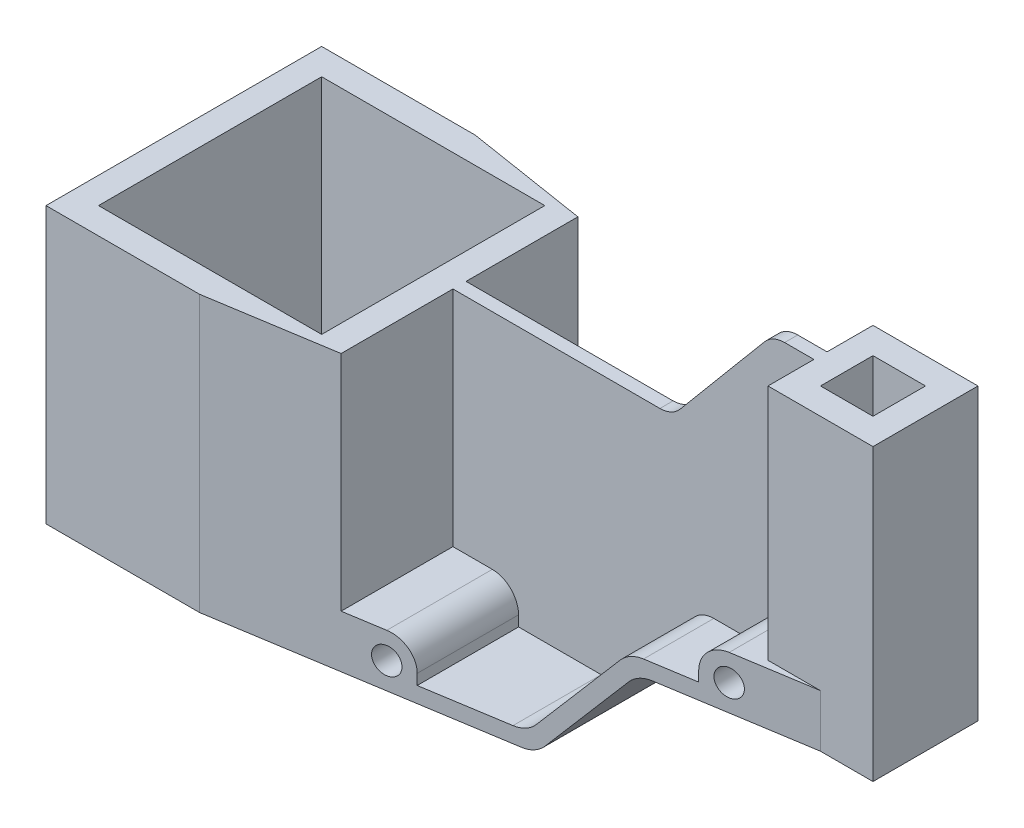
SolidWorks part; units mm, degrees
material "1060 Alloy"
ref_plane "Front Plane" through (0, 0, 0) normal (0, 0, 1) x (1, 0, 0)
ref_plane "Top Plane" through (0, 0, 0) normal (0, 1, 0) x (1, 0, 0)
ref_plane "Right Plane" through (0, 0, 0) normal (1, 0, 0) x (0, 0, -1)
sketch "Sketch1" plane through (0, 0, 0) normal (0, 0, 1) x (1, 0, 0)
  line L1 (-47.8306, 122.7704) -> (234.6694, 122.7704)
  line L2 (-47.8306, 122.7704) -> (-47.8306, -27.7296)
  line L3 (-47.8306, -27.7296) -> (234.6694, -27.7296)
  line L4 (234.6694, 122.7704) -> (234.6694, -27.7296)
extrude "Boss-Extrude2" add sketch "Sketch1" along normal blind 105
sketch "Sketch16" plane through (0, 0, 105) normal (0, 0, 1) x (1, 0, 0)
  line L5 (234.6694, -27.7296) -> (154.6694, -27.7296)
  line L6 (234.6694, -27.7296) -> (234.6694, 12.2704)
  line L7 (234.6694, 12.2704) -> (154.6694, 12.2704)
  line L8 (154.6694, -27.7296) -> (154.6694, 12.2704)
  line L13 (82.1694, 77.2704) -> (-47.8306, 77.2704)
  line L14 (82.1694, 77.2704) -> (82.1694, 122.7704)
  line L15 (82.1694, 122.7704) -> (-47.8306, 122.7704)
  line L16 (-47.8306, 77.2704) -> (-47.8306, 122.7704)
extrude "Cut-Extrude10" cut sketch "Sketch16" against normal blind 105
sketch "Sketch17" plane through (0, 122.7704, 0) normal (0, 1, 0) x (1, 0, 0)
  line L0 (234.6694, -105) -> (234.6694, 0) construction
  line L10 (214.6694, -32.5) -> (234.6694, -32.5)
  line L11 (214.6694, -32.5) -> (214.6694, 0)
  line L12 (214.6694, 0) -> (234.6694, 0)
  line L13 (234.6694, -32.5) -> (234.6694, 0)
  line L14 (214.6694, -72.5) -> (234.6694, -72.5)
  line L15 (214.6694, -72.5) -> (214.6694, -105)
  line L16 (214.6694, -105) -> (234.6694, -105)
  line L17 (234.6694, -72.5) -> (234.6694, -105)
extrude "Cut-Extrude11" cut sketch "Sketch17" against normal blind 110.5
sketch "Sketch18" plane through (0, 122.7704, 0) normal (0, 1, 0) x (1, 0, 0)
  line L0 (214.6694, -32.5) -> (194.6694, -32.5)
  line L1 (194.6694, -32.5) -> (194.6694, -50)
  line L2 (194.6694, -50) -> (82.1694, -50)
  line L3 (82.1694, 0) -> (82.1694, -105) construction
  line L4 (82.1694, -50) -> (82.1694, 0)
  line L5 (82.1694, 0) -> (214.6694, 0)
  line L6 (214.6694, 0) -> (214.6694, -32.5)
  line L7 (214.6694, -72.5) -> (194.6694, -72.5)
  line L8 (194.6694, -72.5) -> (194.6694, -55)
  line L9 (194.6694, -55) -> (82.1694, -55)
  line L10 (82.1694, -55) -> (82.1694, -105)
  line L11 (82.1694, -105) -> (214.6694, -105)
  line L12 (214.6694, -105) -> (214.6694, -72.5)
extrude "Cut-Extrude12" cut sketch "Sketch18" against normal blind 90.5
sketch "Sketch19" plane through (0, 32.2704, 0) normal (0, 1, 0) x (1, 0, 0)
  line L6 (194.6694, -55) -> (82.1694, -55) construction
  line L7 (174.6694, -55) -> (82.1694, -55)
  line L8 (82.1694, -55) -> (82.1694, -105)
  line L9 (82.1694, -105) -> (174.6694, -105)
  line L10 (82.1694, -105) -> (214.6694, -105) construction
  line L11 (174.6694, -105) -> (174.6694, -55)
extrude "Cut-Extrude13" cut sketch "Sketch19" against normal blind 14
sketch "Sketch20" plane through (0, 32.2704, 0) normal (0, 1, 0) x (1, 0, 0)
  line L0 (174.6694, -50) -> (174.6694, 0)
  line L1 (82.1694, -50) -> (194.6694, -50) construction
  line L2 (214.6694, 0) -> (82.1694, 0) construction
  line L3 (174.6694, 0) -> (82.1694, 0)
  line L4 (82.1694, 0) -> (82.1694, -50)
  line L5 (82.1694, -50) -> (174.6694, -50)
extrude "Cut-Extrude14" cut sketch "Sketch20" against normal blind 14
sketch "Sketch21" plane through (0, 77.2704, 0) normal (0, 1, 0) x (1, 0, 0)
  line L0 (-47.8306, 0) -> (82.1694, 0) construction
  line L1 (82.1694, -50) -> (57.1694, -50)
  line L2 (82.1694, -50) -> (82.1694, 0)
  line L3 (82.1694, 0) -> (57.1694, 0)
  line L4 (57.1694, -50) -> (57.1694, 0)
  line L5 (82.1694, -55) -> (82.1694, -105) construction
  line L6 (82.1694, -55) -> (57.1694, -55)
  line L7 (82.1694, -55) -> (82.1694, -105)
  line L8 (82.1694, -105) -> (57.1694, -105)
  line L9 (57.1694, -55) -> (57.1694, -105)
  line L10 (82.1694, -55) -> (82.1694, -105) construction
  line L11 (-47.8306, -105) -> (82.1694, -105) construction
extrude "Cut-Extrude15" cut sketch "Sketch21" against normal blind 85
sketch "Sketch22" plane through (0, 77.2704, 0) normal (0, 1, 0) x (1, 0, 0)
  line L0 (-37.8306, -10) -> (-37.8306, -95)
  line L1 (-47.8306, 0) -> (57.1694, 0)
  line L2 (-47.8306, 0) -> (-47.8306, -105)
  line L3 (-47.8306, -105) -> (57.1694, -105)
  line L4 (57.1694, 0) -> (57.1694, -105)
  line L5 (-37.8306, -95) -> (47.1694, -95)
  line L6 (47.1694, -10) -> (47.1694, -95)
  line L7 (-37.8306, -10) -> (47.1694, -10)
  dimension "D1" = 10
extrude "Cut-Extrude16" cut sketch "Sketch22" against normal blind 105 contours L0 L5 L6 L7
sketch "Sketch24" plane through (0, 0, 105) normal (0, 0, 1) x (1, 0, 0)
  line L0 (154.6694, 12.2704) -> (121.1054, -27.7296)
  line L3 (151.8715, 18.2704) -> (118.3076, -21.7296)
  line L4 (-47.8306, -27.7296) -> (154.6694, -27.7296) construction
  line L5 (82.1694, -7.7296) -> (82.1694, -21.7296)
  line L6 (82.1694, -21.7296) -> (118.3076, -21.7296)
  line L7 (174.6694, 18.2704) -> (82.1694, 18.2704) construction
  line L8 (151.8715, 18.2704) -> (82.1694, 18.2704)
  line L9 (82.1694, 18.2704) -> (82.1694, -7.7296)
  dimension "D1" = 14
  dimension "D2" = 6
  dimension "D3" = 130
extrude "Cut-Extrude17" cut sketch "Sketch24" against normal blind 50 contours L8 L9 L5 L6 L3
sketch "Sketch25" plane through (0, 0, 105) normal (0, 0, 1) x (1, 0, 0)
  line L0 (118.3076, -21.7296) -> (151.8715, 18.2704)
  line L1 (154.6694, -27.7296) -> (154.6694, 12.2704)
  line L2 (154.6694, 12.2704) -> (121.1054, -27.7296)
  line L3 (-47.8306, -27.7296) -> (154.6694, -27.7296) construction
  line L4 (154.6694, -27.7296) -> (121.1054, -27.7296)
extrude "Cut-Extrude18" cut sketch "Sketch25" against normal blind 120 contours L4 L2 L1
sketch "Sketch26" plane through (0, 0, 0) normal (0, 0, -1) x (-1, 0, 0)
  line L0 (-82.1694, -7.7296) -> (-82.1694, -21.7296)
  line L1 (-82.1694, -21.7296) -> (-118.3076, -21.7296)
  line L2 (-118.3076, -21.7296) -> (-151.8715, 18.2704)
  line L3 (-82.1694, 18.2704) -> (-174.6694, 18.2704) construction
  line L5 (-121.1054, -27.7296) -> (-154.6694, 12.2704)
  line L6 (-151.8715, 18.2704) -> (-82.1694, 18.2704)
  line L7 (-82.1694, 18.2704) -> (-82.1694, -7.7296)
  dimension "D2" = 14
extrude "Cut-Extrude19" cut sketch "Sketch26" against normal blind 50 contours L7 L0 L1 L2 L6
sketch "Sketch27" plane through (0, 0, 0) normal (0, 0, -1) x (-1, 0, 0)
  circle A0 centre (-184.6694, 22.2704) radius 5
  circle A1 centre (-72.1694, -17.7296) radius 5
extrude "Cut-Extrude20" cut sketch "Sketch27" against normal blind 120
sketch "Sketch28" plane through (0, -27.7296, 0) normal (0, -1, 0) x (1, 0, 0)
  line L0 (10.6694, 105) -> (214.6694, 105)
  line L2 (-47.8306, 105) -> (121.1054, 105) construction
  line L3 (214.6694, 105) -> (214.6694, 72.5)
  line L4 (10.6694, 105) -> (214.6694, 72.5)
  line L6 (214.6694, 32.5) -> (10.6694, 0)
  line L7 (-47.8306, 0) -> (121.1054, 0) construction
  line L9 (214.6694, 32.5) -> (214.6694, 0)
  line L10 (214.6694, 0) -> (10.6694, 0)
extrude "Cut-Extrude21" cut sketch "Sketch28" against normal blind 160
fillet "Fillet1" radius 10 4 edges at (82.1694, -7.7296, 30.6955) (174.6694, 32.2704, 38.0637) (174.6694, 32.2704, 66.9363) (82.1694, -7.7296, 74.3045)
fillet "Fillet2" radius 10 6 edges at (121.1054, -27.7296, 52.5) (118.3076, -21.7296, 71.4259) (154.6694, 12.2704, 52.5) (151.8715, 18.2704, 36.2477) (151.8715, 18.2704, 68.7523) (118.3076, -21.7296, 33.5741)
sketch "Sketch29" plane through (0, 0, 55) normal (0, 0, 1) x (1, 0, 0)
  line L3 (82.1694, 77.2704) -> (140.677, 77.2704)
  line L5 (194.6694, 122.7704) -> (82.1694, 122.7704) construction
  line L6 (82.1694, 122.7704) -> (178.856, 122.7704)
  line L7 (140.677, 77.2704) -> (178.856, 122.7704)
  line L8 (82.1694, 122.7704) -> (82.1694, 77.2704)
extrude "Cut-Extrude22" cut sketch "Sketch29" against normal blind 160
fillet "Fillet3" radius 10 2 edges at (178.856, 122.7704, 52.5) (140.677, 77.2704, 52.5)
sketch "Sketch30" plane through (0, 122.7704, 0) normal (0, 1, 0) x (1, 0, 0)
  line L0 (224.6694, -42.5) -> (224.6694, -62.5)
  line L1 (234.6694, -32.5) -> (194.6694, -32.5)
  line L2 (234.6694, -32.5) -> (234.6694, -72.5)
  line L3 (234.6694, -72.5) -> (194.6694, -72.5)
  line L4 (194.6694, -32.5) -> (194.6694, -72.5)
  line L5 (224.6694, -62.5) -> (204.6694, -62.5)
  line L6 (204.6694, -42.5) -> (204.6694, -62.5)
  line L7 (224.6694, -42.5) -> (204.6694, -42.5)
  dimension "D1" = 10
extrude "Cut-Extrude23" cut sketch "Sketch30" against normal blind 160 contours L0 L5 L6 L7
sketch "Sketch31" plane through (0, 0, 0) normal (0, 1, 0) x (1, 0, 0)
  line L0 (-72.4502, -52.5) -> (265.4395, -52.5) construction
  line L1 (4.6694, 26.1103) -> (4.6694, -129.5727) construction
  line L2 (-47.8306, 0) -> (-47.8306, -105) construction
  line L3 (57.1694, -7.4081) -> (57.1694, -50) construction
  line L4 (-37.8306, -10) -> (47.1694, -10) construction
  line L5 (-47.8306, 0) -> (10.6694, 0) construction
  line L6 (-37.8306, -10) -> (-37.8306, -95) construction
  line L7 (57.1694, -55) -> (57.1694, -97.5919) construction
  line L8 (47.1694, -10) -> (47.1694, -95) construction
  line L9 (82.1694, -50) -> (113.6445, -50) construction
  line L10 (136.0139, -55) -> (57.1694, -55) construction
  line L11 (234.6694, -72.5) -> (234.6694, -32.5) construction
  line L12 (194.6694, -50) -> (194.6694, -32.5) construction
  line L15 (204.6694, -42.5) -> (204.6694, -62.5) construction
  line L16 (224.6694, -42.5) -> (224.6694, -62.5) construction
  line L17 (214.6694, -129.5727) -> (214.6694, 26.1103) construction
  dimension "D1" = 52.5
  dimension "D2" = 52.5
  dimension "D3" = 105
  dimension "D4" = 52.5
  dimension "D5" = 10
  dimension "D6" = 10
  dimension "D7" = 10
  dimension "D8" = 5
  dimension "D9" = 2.5
  dimension "D10" = 40
  dimension "D11" = 20
  dimension "D12" = 210
sketch "Sketch32" plane through (0, 0, 0) normal (0, 0, 1) x (1, 0, 0)
  line L0 (-47.8306, 77.2704) -> (-47.8306, -27.7296) construction
  line L1 (-47.8306, 77.2704) -> (-47.8306, -27.7296)
  line L2 (-47.8306, 77.2704) -> (57.1694, 77.2704)
  line L3 (57.1694, 77.2704) -> (57.1694, -7.7296)
  line L4 (10.6694, -27.7296) -> (116.4423, -27.7296) construction
  line L5 (82.1694, -17.7296) -> (82.1694, -21.7296) construction
  line L6 (148.8742, 14.6982) -> (121.3049, -18.1575) construction
  line L7 (151.672, 8.6982) -> (124.1028, -24.1575) construction
  line L8 (194.6694, 32.2704) -> (194.6694, 122.7704) construction
  line L9 (234.6694, 12.2704) -> (234.6694, 122.7704) construction
  line L10 (214.6694, 12.2704) -> (214.6694, 32.2704) construction
  line L11 (214.6694, 32.2704) -> (194.6694, 32.2704) construction
  line L12 (214.6694, 12.2704) -> (159.3325, 12.2704) construction
  line L13 (143.6743, 80.8425) -> (175.8586, 119.1982) construction
  line L14 (82.1694, -21.7296) -> (113.6445, -21.7296) construction
  dimension "D4" = 6
  dimension "D1" = 105
  dimension "D2" = 105
  dimension "D3" = 130
  dimension "D5" = 10
  dimension "D6" = 120
  dimension "D7" = 6
  dimension "D8" = 40
  dimension "D9" = 20
  dimension "D10" = 20
  dimension "D11" = 40
  dimension "D12" = 52.5
  dimension "D13" = 50
  dimension "D14" = 130
